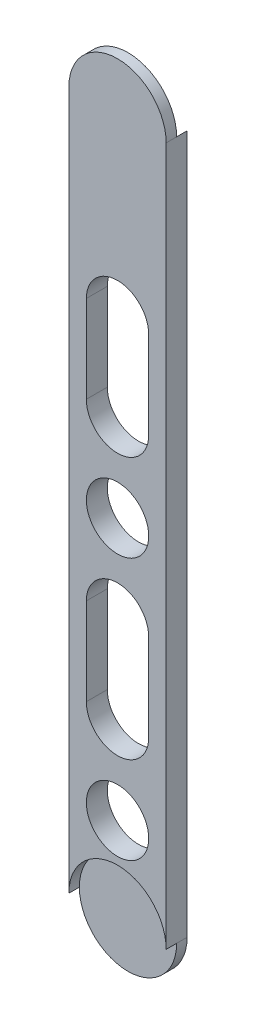
SolidWorks part; units mm, degrees
ref_plane "Plan de face" through (0, 0, 0) normal (0, 0, 1) x (1, 0, 0)
ref_plane "Plan de dessus" through (0, 0, 0) normal (0, 1, 0) x (1, 0, 0)
ref_plane "Plan de droite" through (0, 0, 0) normal (1, 0, 0) x (0, 0, -1)
sketch "Esquisse1" plane through (0, 0, 0) normal (0, 0, 1) x (1, 0, 0)
  line L1 (27.1171, 190.9191) -> (54.9671, 190.9191)
  line L2 (27.1171, 190.9191) -> (27.1171, -9.0809)
  line L3 (27.1171, -9.0809) -> (54.9671, -9.0809)
  line L4 (54.9671, 190.9191) -> (54.9671, -9.0809)
  arc A0 (27.1171, -9.0809) -> (54.9671, -9.0809) centre (41.0421, -9.0809) ccw
  arc A1 (27.1171, 190.9191) -> (54.9671, 190.9191) centre (41.0421, 190.9191) cw
  dimension "D1" = 27.85
  dimension "D2" = 200
extrude "Boss.-Extru.1" add sketch "Esquisse1" along normal blind 6 contours L4 L1 L2 L3 | L3 A0 | A1 L1
sketch "Esquisse2" plane through (0, 0, 6) normal (0, 0, 1) x (1, 0, 0)
  circle A0 centre (41.0421, -9.0809) radius 13.925
extrude "Enlèv. mat.-Extru.1" cut sketch "Esquisse2" against normal blind 3
sketch "Esquisse3" plane through (0, 0, 0) normal (0, 0, -1) x (-1, 0, 0)
  circle A0 centre (-41.0421, 190.9191) radius 13.925
extrude "Enlèv. mat.-Extru.2" cut sketch "Esquisse3" against normal blind 3
sketch "Esquisse4" plane through (0, 0, 6) normal (0, 0, 1) x (1, 0, 0)
  line L1 (31.2921, 200.6691) -> (50.7921, 200.6691)
  line L2 (31.2921, 200.6691) -> (31.2921, 160.1691)
  line L3 (31.2921, 160.1691) -> (50.7921, 160.1691)
  line L4 (50.7921, 200.6691) -> (50.7921, 160.1691)
  line L5 (54.9671, 190.9191) -> (54.9671, -9.0809) construction
  circle A0 centre (41.0421, 190.9191) radius 2.5
  arc A1 (54.9671, 190.9191) -> (27.1171, 190.9191) centre (41.0421, 190.9191) ccw construction
  dimension "D4" = 9.75
  dimension "D5" = 9.75
  dimension "D6" = 0
  dimension "D1" = 19.5
  dimension "D2" = 40.5
  dimension "D3" = 4.175
sketch "Esquisse5" plane through (0, 0, 6) normal (0, 0, 1) x (1, 0, 0)
  line L0 (54.9671, 190.9191) -> (54.9671, -9.0809) construction
  line L1 (32.1171, 65.9191) -> (49.9671, 65.9191)
  line L2 (32.1171, 65.9191) -> (32.1171, 40.9191)
  line L3 (32.1171, 40.9191) -> (49.9671, 40.9191)
  line L4 (49.9671, 65.9191) -> (49.9671, 40.9191)
  line L5 (32.1171, 140.9191) -> (49.9671, 140.9191)
  line L6 (32.1171, 140.9191) -> (32.1171, 115.9191)
  line L7 (32.1171, 115.9191) -> (49.9671, 115.9191)
  line L8 (49.9671, 140.9191) -> (49.9671, 115.9191)
  line L9 (27.1171, 190.9191) -> (27.1171, -9.0809) construction
  circle A0 centre (41.0421, 90.9191) radius 8.925
  circle A1 centre (41.0421, 15.9191) radius 8.925
  arc A2 (32.1171, 140.9191) -> (49.9671, 140.9191) centre (41.0421, 140.9191) cw
  arc A3 (49.9671, 115.9191) -> (32.1171, 115.9191) centre (41.0421, 115.9191) cw
  arc A4 (32.1171, 65.9191) -> (49.9671, 65.9191) centre (41.0421, 65.9191) cw
  arc A5 (32.1171, 40.9191) -> (49.9671, 40.9191) centre (41.0421, 40.9191) ccw
  arc A6 (27.1171, -9.0809) -> (54.9671, -9.0809) centre (41.0421, -9.0809) ccw construction
  arc A7 (54.9671, -9.0809) -> (27.1171, -9.0809) centre (41.0421, -9.0809) ccw construction
  dimension "D5" = 17.85
  dimension "D6" = 17.85
  dimension "D8" = 25
  dimension "D12" = 25
  dimension "D1" = 5
  dimension "D2" = 5
  dimension "D3" = 5
  dimension "D4" = 5
  dimension "D7" = 0
  dimension "D9" = 25
  dimension "D10" = 50
  dimension "D11" = 0
  dimension "D13" = 25
  dimension "D14" = 50
extrude "Enlèv. mat.-Extru.3" cut sketch "Esquisse5" against normal blind 10 contours A2 L5 | L8 L5 L6 L7 | A3 L7 | A0 | A4 L1 | L4 L1 L2 L3 | L3 A5 | A1
